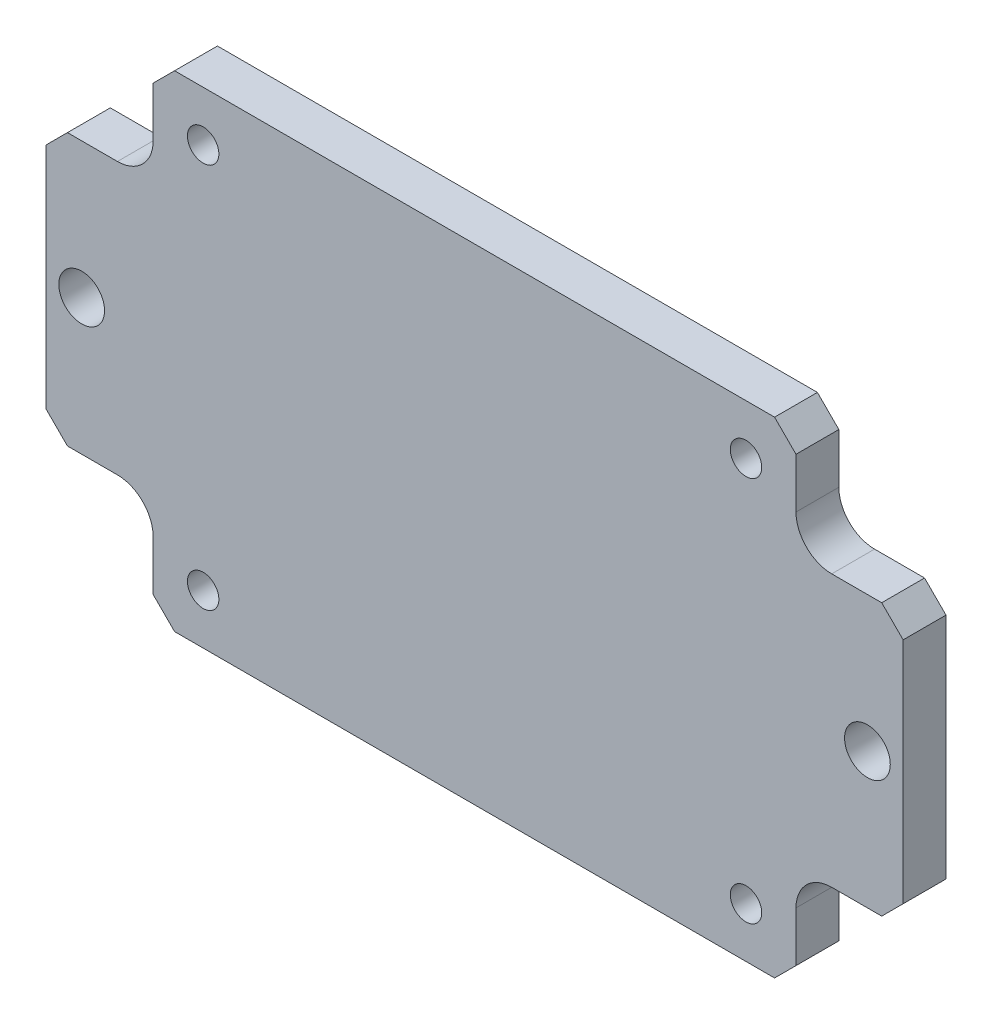
SolidWorks part; units mm, degrees
material "7075-T6 (SN)"
ref_plane "Front Plane" through (0, 0, 0) normal (0, 0, 1) x (1, 0, 0)
ref_plane "Top Plane" through (0, 0, 0) normal (0, 1, 0) x (1, 0, 0)
ref_plane "Right Plane" through (0, 0, 0) normal (1, 0, 0) x (0, 0, -1)
sketch "Sketch1" plane through (0, 0, 0) normal (0, 0, 1) x (1, 0, 0)
  line L1 (-30, -17) -> (30, -17)
  line L2 (-30, -17) -> (-30, 17)
  line L3 (-30, 17) -> (30, 17)
  line L4 (30, -17) -> (30, 17)
  line L5 (-30, -17) -> (30, 17) construction
  line L6 (-30, 17) -> (30, -17) construction
  point P0 (0, 0)
  dimension "D1" = 34
  dimension "D2" = 60
extrude "Boss-Extrude1" add sketch "Sketch1" along normal blind 3
sketch "Sketch2" plane through (0, 0, 3) normal (0, 0, 1) x (1, 0, 0)
  line L0 (21, 17) -> (22.5, 15.5)
  line L1 (30, 17) -> (-30, 17) construction
  line L2 (22.5, 15.5) -> (22.5, 12)
  line L3 (25, 9.5) -> (28.5, 9.5)
  line L4 (28.5, 9.5) -> (30, 8)
  line L5 (30, -17) -> (30, 17) construction
  line L6 (30, 8) -> (30, 17)
  line L7 (30, 17) -> (21, 17)
  line L8 (0, 17) -> (0, -17) construction
  line L9 (-30, -17) -> (30, -17) construction
  line L10 (-30, 17) -> (-21, 17)
  line L11 (30, 0) -> (-30, 0) construction
  line L12 (-30, 17) -> (-30, -17) construction
  line L13 (-30, 8) -> (-30, 17)
  line L14 (-28.5, 9.5) -> (-30, 8)
  line L15 (-25, 9.5) -> (-28.5, 9.5)
  line L16 (-22.5, 15.5) -> (-22.5, 12)
  line L17 (-21, 17) -> (-22.5, 15.5)
  line L18 (30, -8) -> (30, -17)
  line L19 (28.5, -9.5) -> (30, -8)
  line L20 (25, -9.5) -> (28.5, -9.5)
  line L21 (22.5, -15.5) -> (22.5, -12)
  line L22 (21, -17) -> (22.5, -15.5)
  line L23 (30, -17) -> (21, -17)
  line L24 (-22.5, -15.5) -> (-22.5, -12)
  line L25 (-21, -17) -> (-22.5, -15.5)
  line L26 (-30, -17) -> (-21, -17)
  line L27 (-30, -8) -> (-30, -17)
  line L28 (-28.5, -9.5) -> (-30, -8)
  line L29 (-25, -9.5) -> (-28.5, -9.5)
  arc A0 (22.5, 12) -> (25, 9.5) centre (25, 12) ccw
  arc A1 (-22.5, 12) -> (-25, 9.5) centre (-25, 12) cw
  arc A2 (22.5, -12) -> (25, -9.5) centre (25, -12) cw
  arc A3 (-22.5, -12) -> (-25, -9.5) centre (-25, -12) ccw
  point P13 (22.5, 9.5)
  point P31 (-22.5, 9.5)
  dimension "D3" = 2.5
  dimension "D1" = 9
  dimension "D2" = 6
extrude "Cut-Extrude1" cut sketch "Sketch2" against normal up to next
hole_wizard "M2 Clearance Hole1" positions "Sketch3" profile "Sketch4" hole size "M2" standard "DIN" end condition up to next
sketch "Sketch3" plane through (0, 0, 3) normal (0, 0, 1) x (1, 0, 0)
  line L1 (-19, -13.5) -> (19, -13.5) construction
  line L2 (-19, -13.5) -> (-19, 13.5) construction
  line L3 (-19, 13.5) -> (19, 13.5) construction
  line L4 (19, -13.5) -> (19, 13.5) construction
  line L5 (-19, -13.5) -> (19, 13.5) construction
  line L6 (-19, 13.5) -> (19, -13.5) construction
  line L7 (21, 17) -> (-21, 17) construction
  line L8 (-22.5, 12) -> (-22.5, 15.5) construction
  point P11 (19, 13.5)
  point P48 (-19, -13.5)
  point P49 (-19, 13.5)
  point P50 (19, -13.5)
  dimension "D1" = 3.5
  dimension "D2" = 3.5
sketch "Sketch4" plane through (19, 13.5, 3) normal (1, 0, 0) x (0, -1, 0)
  line L0 (0, 0) -> (0, 3)
  line L1 (0, 3) -> (1.1, 3)
  line L2 (1.1, 3) -> (1.1, 0)
  line L5 (1.1, 0) -> (0, 0)
  line L11 (0, -6.35) -> (0, 107.95) construction
  dimension "Thru Hole Dia." = 2.2
  dimension "Thru Hole Depth" = 3
hole_wizard "M3 Clearance Hole1" positions "Sketch5" profile "Sketch6" hole size "M3" standard "DIN" end condition up to next
sketch "Sketch5" plane through (0, 0, 3) normal (0, 0, 1) x (1, 0, 0)
  line L0 (-30, 8) -> (-30, -8) construction
  line L1 (30, -8) -> (30, 8) construction
  point P0 (-27.5, 0)
  point P2 (27.5, 0)
  dimension "D1" = 2.5
  dimension "D2" = 2.5
sketch "Sketch6" plane through (-27.5, 0, 3) normal (1, 0, 0) x (0, -1, 0)
  line L0 (0, 0) -> (0, 3)
  line L1 (0, 3) -> (1.6, 3)
  line L2 (1.6, 3) -> (1.6, 0)
  line L5 (1.6, 0) -> (0, 0)
  line L11 (0, -6.35) -> (0, 107.95) construction
  dimension "Thru Hole Dia." = 3.2
  dimension "Thru Hole Depth" = 3
sketch "Sketch7" plane through (0, 0, 0) normal (0, 0, -1) x (-1, 0, 0)
  line L5 (-7.5, -13) -> (7.5, -13)
  line L6 (-25, -3) -> (-25, 3)
  line L7 (25, -3) -> (25, 3)
  line L35 (-30, -8) -> (-30, 8) construction
  line L36 (21, -17) -> (-21, -17) construction
  line L37 (0, -13) -> (0, 0) construction
  line L38 (0, 0) -> (-25, 0) construction
  line L39 (-7.5, 13) -> (7.5, 13)
  arc A0 (-7.5, -13) -> (-25, -3) centre (-7.5, 7.3125) cw
  arc A1 (-7.5, 13) -> (-25, 3) centre (-7.5, -7.3125) ccw
  arc A2 (7.5, -13) -> (25, -3) centre (7.5, 7.3125) ccw
  arc A3 (7.5, 13) -> (25, 3) centre (7.5, -7.3125) cw
  point P20 (0, 13)
  dimension "D1" = 7.5
  dimension "D2" = 5
  dimension "D3" = 3
  dimension "D4" = 4
extrude "Cut-Extrude2" cut sketch "Sketch7" against normal blind 0.2
fillet "Fillet2" radius 4 4 edges at (-25, -3, 0.1) (-25, 3, 0.1) (25, -3, 0.1) (25, 3, 0.1)
